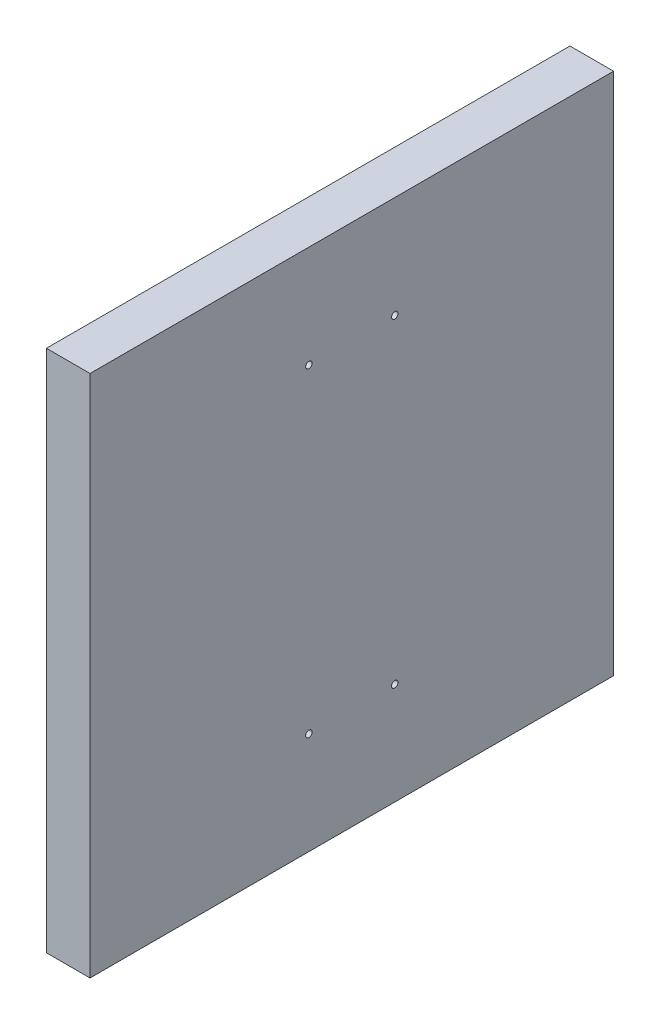
SolidWorks part; units mm, degrees
ref_plane "Front Plane" through (0, 0, 0) normal (0, 0, 1) x (1, 0, 0)
ref_plane "Top Plane" through (0, 0, 0) normal (0, 1, 0) x (1, 0, 0)
ref_plane "Right Plane" through (0, 0, 0) normal (1, 0, 0) x (0, 0, -1)
sketch "Sketch1" plane through (0, 0, 0) normal (1, 0, 0) x (0, 0, -1)
  line L1 (-152.4, -152.4) -> (152.4, -152.4)
  line L2 (-152.4, -152.4) -> (-152.4, 152.4)
  line L3 (-152.4, 152.4) -> (152.4, 152.4)
  line L4 (152.4, -152.4) -> (152.4, 152.4)
  dimension "D1" = 304.8
  dimension "D2" = 152.4
  dimension "D3" = 152.4
extrude "Boss-Extrude1" add sketch "Sketch1" along normal blind 25.4
sketch "Sketch3" plane through (25.4, 0, 0) normal (1, 0, 0) x (0, 0, -1)
  line L0 (0, 0) -> (0, 24.9845) construction
  line L1 (0, 0) -> (23.8874, 0) construction
  circle A0 centre (-25, -93) radius 1.875
  circle A1 centre (25, -93) radius 1.875
  circle A2 centre (-25, 93) radius 1.875
  circle A3 centre (25, 93) radius 1.875
  dimension "D1" = 3.75
  dimension "D2" = 93
  dimension "D3" = 25
extrude "Cut-Extrude1" cut sketch "Sketch3" against normal through all
